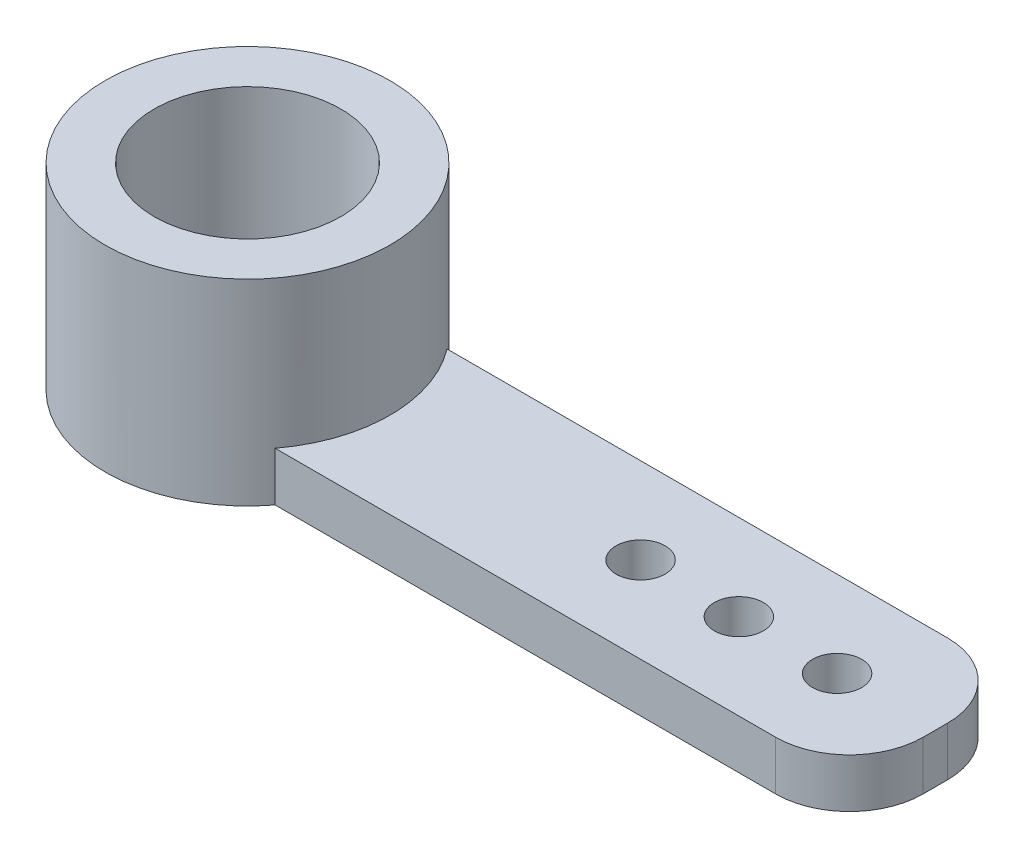
SolidWorks part; units mm, degrees
ref_plane "Front" through (0, 0, 0) normal (0, 0, 1) x (1, 0, 0)
ref_plane "Top" through (0, 0, 0) normal (0, 1, 0) x (1, 0, 0)
ref_plane "Right" through (0, 0, 0) normal (1, 0, 0) x (0, 0, -1)
sketch "草图1" plane through (0, 0, 0) normal (0, 1, 0) x (1, 0, 0)
  line L0 (-12.8608, 0) -> (15.3394, 0) construction
  circle A0 centre (0, 0) radius 2.9
  dimension "D1" = 5.8
extrude "凸台-拉伸1" add sketch "草图1" along normal blind 4
sketch "草图2" plane through (0, 0, 0) normal (0, 1, 0) x (1, 0, 0)
  line L0 (-6.7906, 0) -> (11.2096, 0) construction
  line L2 (14, -1.75) -> (1.3719, -1.75)
  line L3 (14, -1.75) -> (14, 1.75)
  line L4 (14, 1.75) -> (1.3719, 1.75)
  line L5 (1.3719, -1.75) -> (1.3719, 1.75)
  line L6 (14, -1.75) -> (1.3719, 1.75) construction
  line L7 (14, 1.75) -> (1.3719, -1.75) construction
  point P3 (7.686, 0)
  dimension "D1" = 3.5
  dimension "D2" = 14
extrude "凸台-拉伸2" add sketch "草图2" along normal blind 1
sketch "草图3" plane through (0, 0, 0) normal (0, 1, 0) x (1, 0, 0)
  line L0 (-7.4712, 0) -> (17.1185, 0) construction
  circle A0 centre (8, 0) radius 0.5
  circle A1 centre (12, 0) radius 0.5
  circle A2 centre (10, 0) radius 0.5
  circle A3 centre (0, 0) radius 1
  dimension "D1" = 1
  dimension "D2" = 1
  dimension "D3" = 1
  dimension "D7" = 2
  dimension "D4" = 8
  dimension "D5" = 2
  dimension "D6" = 2
extrude "切除-拉伸1" cut sketch "草图3" along normal through all
fillet "圆角1" radius 1.5 2 edges at (14, 0.5, 1.75) (14, 0.5, -1.75)
sketch "草图4" plane through (0, 4, 0) normal (0, 1, 0) x (1, 0, 0)
  circle A0 centre (0, 0) radius 1.9
  dimension "D1" = 3.8
extrude "切除-拉伸2" cut sketch "草图4" against normal blind 3
